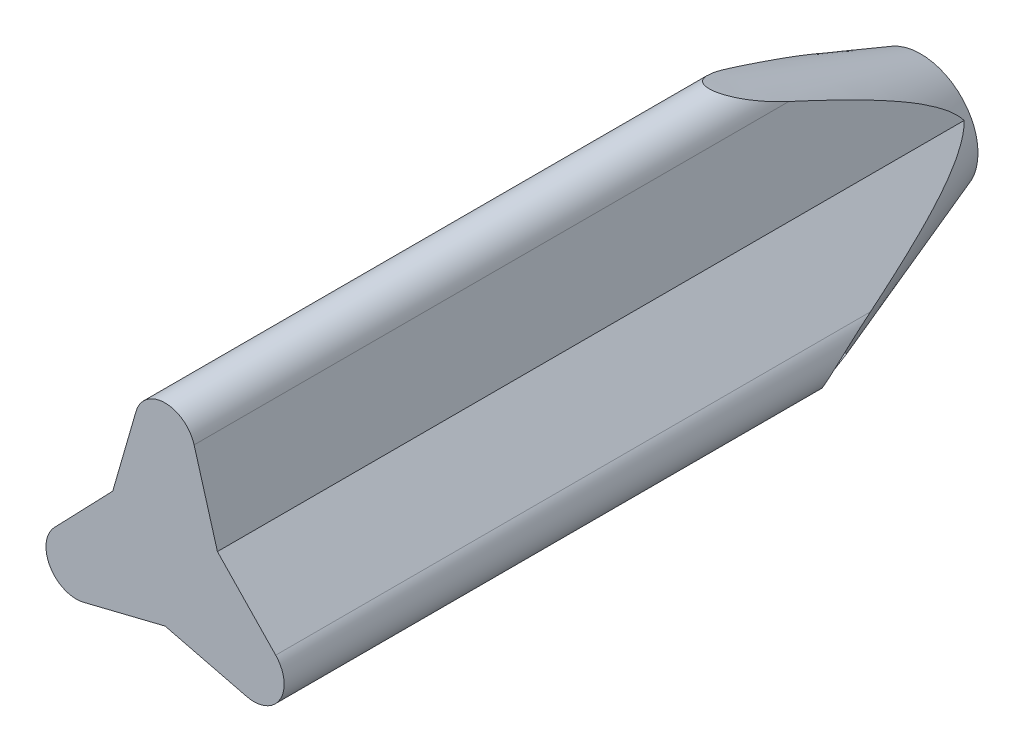
SolidWorks part; units mm, degrees
material "ABS"
ref_plane "Front Plane" through (0, 0, 0) normal (0, 0, 1) x (1, 0, 0)
ref_plane "Top Plane" through (0, 0, 0) normal (0, 1, 0) x (1, 0, 0)
ref_plane "Right Plane" through (0, 0, 0) normal (1, 0, 0) x (0, 0, -1)
sketch "Sketch1" plane through (0, 0, 0) normal (0, 0, 1) x (1, 0, 0)
  line L0 (0, 0) -> (0, 14) construction
  line L1 (0, 0) -> (-12.1244, -7) construction
  line L2 (0, 0) -> (12.1244, -7)
  line L3 (-12.1244, -7) -> (-3.4641, 2)
  line L4 (-3.4641, 2) -> (0, 14)
  line L5 (0, 14) -> (3.4641, 2)
  line L6 (0, -4) -> (12.1244, -7)
  line L7 (-12.1244, -7) -> (0, -4)
  line L8 (3.4641, 2) -> (12.1244, -7)
  circle A0 centre (0, 0) radius 14 construction
  circle A1 centre (0, 0) radius 10 construction
  circle A2 centre (0, 0) radius 4 construction
  dimension "D1" = 28
  dimension "D2" = 20
  dimension "D5" = 8
  dimension "D3" = 120
  dimension "D4" = 120
extrude "Boss-Extrude1" add sketch "Sketch1" along normal blind 50
fillet "Fillet1" radius 2 3 edges at (12.1244, -7, 25) (-12.1244, -7, 25) (0, 14, 25)
sketch "Sketch2" plane through (0, 0, 0) normal (1, 0, 0) x (0, 0, -1)
  line L0 (0, 2) -> (0, 3.7889) construction
  line L1 (0, 2) -> (0, 7.3436) construction
  line L2 (-50, 2) -> (0, 2) construction
  line L3 (0, 3.7889) -> (-14, 8.7889)
  line L4 (0, 8.7889) -> (-50, 8.7889) construction
  line L5 (-14, 8.7889) -> (0, 8.7889)
  line L6 (0, 8.7889) -> (0, 3.7889)
  line L7 (0, 3.7889) -> (0, 8.7889)
  line L8 (-14, 8.7889) -> (0, 8.7889)
  dimension "D1" = 14
  dimension "D2" = 5
sketch "Sketch4" plane through (0, 0, 0) normal (1, 0, 0) x (0, 0, -1)
  line L0 (0, 0) -> (7.8198, 0) construction
revolve "Cut-Revolve1" cut sketch "Sketch2" angle 360 about L0
